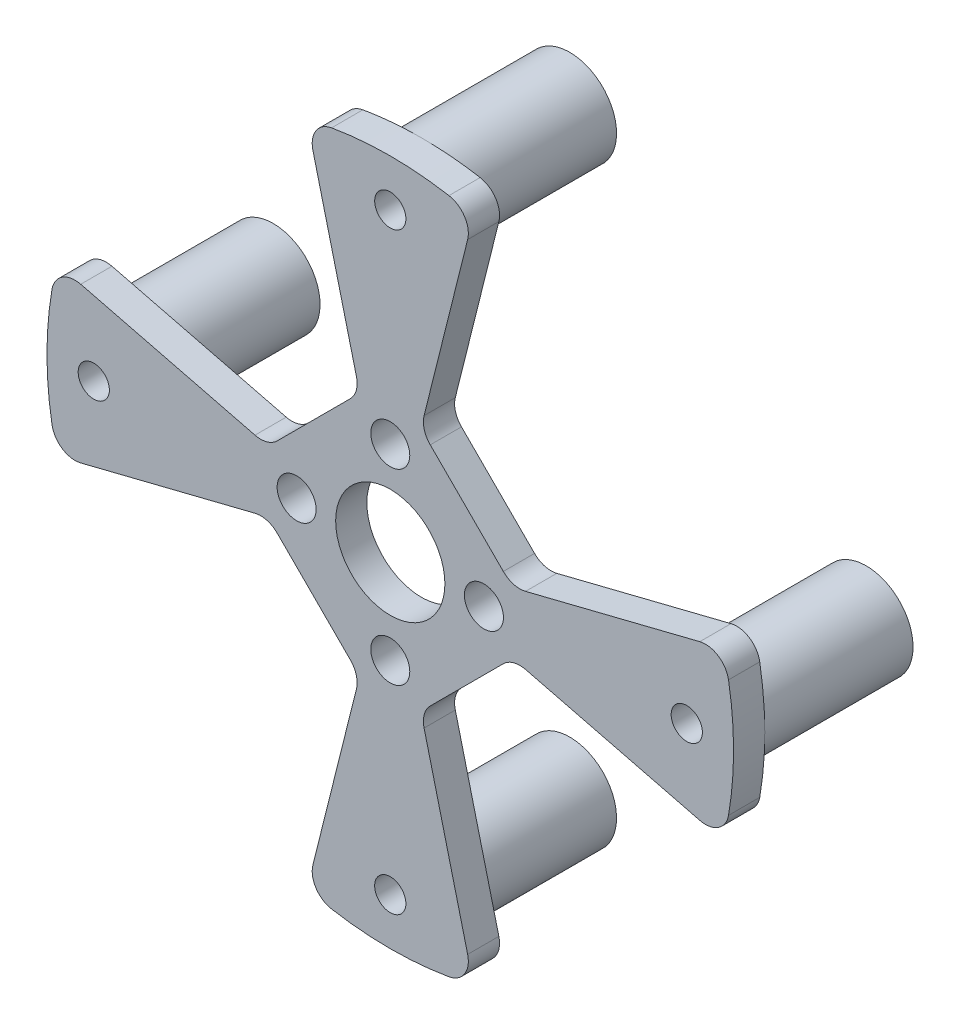
SolidWorks part; units mm, degrees
ref_plane "前视基准面" through (0, 0, 0) normal (0, 0, 1) x (1, 0, 0)
ref_plane "上视基准面" through (0, 0, 0) normal (0, 1, 0) x (1, 0, 0)
ref_plane "右视基准面" through (0, 0, 0) normal (1, 0, 0) x (0, 0, -1)
sketch "草图1" plane through (0, 0, 0) normal (0, 0, 1) x (1, 0, 0)
  circle A0 centre (0, 0) radius 22
extrude "凸台-拉伸1" add sketch "草图1" along normal blind 2
sketch "草图3" plane through (0, 0, 0) normal (0, 0, -1) x (-1, 0, 0)
  line L0 (0, -6) -> (0, 6) construction
  line L1 (6, 6) -> (-6, 6) construction
  line L2 (6, 6) -> (6, -6) construction
  line L3 (6, -6) -> (-6, -6) construction
  line L4 (-6, 6) -> (-6, -6) construction
  line L5 (6, 6) -> (-6, -6) construction
  line L6 (6, -6) -> (-6, 6) construction
  circle A3 centre (6, 0) radius 1.25
  point P0 (0, 0)
extrude "切除-拉伸1" cut sketch "草图3" against normal blind 3
sketch "草图4" plane through (0, 0, 0) normal (0, 0, -1) x (-1, 0, 0)
  circle A0 centre (0, 0) radius 3.5
extrude "切除-拉伸2" cut sketch "草图4" against normal blind 3
sketch "草图6" plane through (0, 0, 0) normal (0, 0, -1) x (-1, 0, 0)
  line L0 (0, -7.5) -> (0, -22) construction
  circle A1 centre (0, 0) radius 22 construction
  circle A2 centre (0, -19) radius 3
extrude "凸台-拉伸3" add sketch "草图6" along normal blind 9.5
sketch "草图8" plane through (0, 0, -9.5) normal (0, 0, -1) x (-1, 0, 0)
  circle A0 centre (0, -19) radius 1
extrude "切除-拉伸4" cut sketch "草图8" along a picked direction on the side against the normal blind 11.5
sketch "草图7" plane through (0, 0, 0) normal (0, 0, -1) x (-1, 0, 0)
  line L0 (-6, 0) -> (0, 6) construction
  line L1 (0, 0) -> (-6, 1.5) construction
  line L2 (-6, 1.5) -> (-25.0731, 6.2683) construction
  line L3 (0, 0) -> (-1.5, 6) construction
  line L4 (-1.5, 6) -> (-6.7018, 26.8073) construction
  line L5 (-1.9613, 7.845) -> (-7.845, 1.9613)
  line L6 (-7.6282, 30.5128) -> (-30.5128, 7.6282)
  line L7 (-7.845, 1.9613) -> (-30.5128, 7.6282)
  line L8 (-7.6282, 30.5128) -> (-1.9613, 7.845)
extrude "切除-拉伸3" cut sketch "草图7" against normal blind 6
pattern_circular "阵列(圆周)1" count 4 over 360 about axis through (0, 0, 0) along (0, 0, 1) of "凸台-拉伸3", "切除-拉伸3", "切除-拉伸4", "切除-拉伸1"
fillet "圆角2" radius 1.5 8 edges at (-21.3431, 5.3358, 1) (-21.3431, -5.3358, 1) (-5.3358, -21.3431, 1) (5.3358, -21.3431, 1) (21.3431, -5.3358, 1) (21.3431, 5.3358, 1) (5.3358, 21.3431, 1) (-5.3358, 21.3431, 1)
fillet "圆角3" radius 1.5 8 edges at (-1.9613, -7.845, 1) (-7.845, -1.9613, 1) (1.9613, -7.845, 1) (7.845, -1.9613, 1) (7.845, 1.9613, 1) (1.9613, 7.845, 1) (-1.9613, 7.845, 1) (-7.845, 1.9613, 1)
